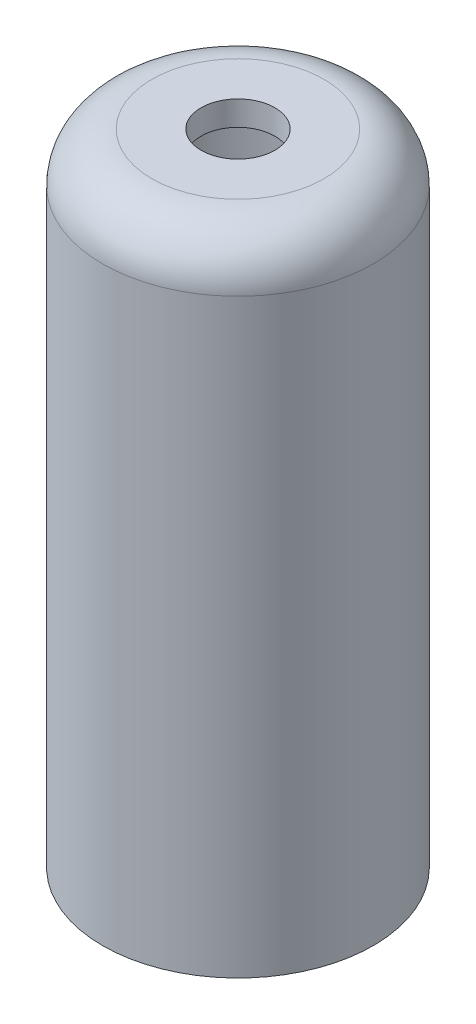
SolidWorks part; units mm, degrees
ref_plane "Front Plane" through (0, 0, 0) normal (0, 0, 1) x (1, 0, 0)
ref_plane "Top Plane" through (0, 0, 0) normal (0, 1, 0) x (1, 0, 0)
ref_plane "Right Plane" through (0, 0, 0) normal (1, 0, 0) x (0, 0, -1)
sketch "Sketch1" plane through (0, 0, 0) normal (0, 1, 0) x (1, 0, 0)
  circle A0 centre (0, 0) radius 17.4625
  dimension "D1" = 34.925
extrude "Boss-Extrude1" add sketch "Sketch1" against normal blind 82.55
sketch "Sketch2" plane through (0, -82.55, 0) normal (0, -1, 0) x (1, 0, 0)
  circle A0 centre (0, 0) radius 14.2875
  dimension "D1" = 28.575
extrude "Cut-Extrude1" cut sketch "Sketch2" against normal blind 79.375
sketch "Sketch3" plane through (0, 0, 0) normal (0, 1, 0) x (1, 0, 0)
  circle A0 centre (0, 0) radius 4.7625
  dimension "D1" = 9.525
extrude "Cut-Extrude2" cut sketch "Sketch3" against normal through all
fillet "Fillet2" radius 6.35 1 edges at (0, 0, 17.4625)
